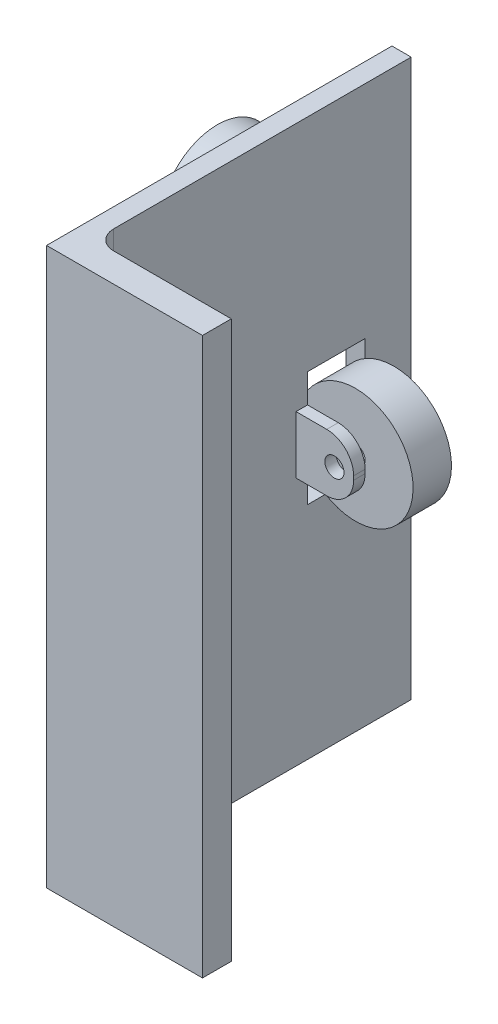
SolidWorks part; units mm, degrees
ref_plane "Front Plane" through (0, 0, 0) normal (0, 0, 1) x (1, 0, 0)
ref_plane "Top Plane" through (0, 0, 0) normal (0, 1, 0) x (1, 0, 0)
ref_plane "Right Plane" through (0, 0, 0) normal (1, 0, 0) x (0, 0, -1)
sketch "Sketch1" plane through (0, 0, 0) normal (0, 1, 0) x (1, 0, 0)
  line L0 (0, 0) -> (0, 90)
  line L1 (0, 90) -> (5, 90)
  line L2 (5, 90) -> (5, 12.5)
  line L3 (10, 7.5) -> (40.625, 7.5)
  line L4 (0, 0) -> (40.625, 0)
  line L5 (40.625, 0) -> (40.625, 7.5)
  arc A0 (5, 12.5) -> (10, 7.5) centre (10, 12.5) ccw
  dimension "D5" = 5
  dimension "D1" = 5
  dimension "D2" = 7.5
  dimension "D3" = 90
  dimension "D4" = 40.625
extrude "Boss-Extrude1" add sketch "Sketch1" along normal blind 145
sketch "Sketch3" plane through (0, 0, 0) normal (-1, 0, 0) x (0, 0, 1)
  line L0 (-90, 145) -> (-90, 0) construction
  line L1 (-90, 145) -> (0, 145) construction
  line L2 (-90, 72.5) -> (0, 72.5) construction
  line L3 (0, 145) -> (0, 0) construction
  circle A0 centre (-54.5, 125) radius 15
  circle A1 centre (-54.5, 20) radius 15
  dimension "D1" = 30
  dimension "D2" = 35.5
  dimension "D3" = 20
extrude "Boss-Extrude2" add sketch "Sketch3" along normal blind 10
sketch "Sketch4" plane through (0, 0, 0) normal (-1, 0, 0) x (0, 0, 1)
  line L2 (-90, 145) -> (-90, 0) construction
  line L3 (-70.5, 108.8445) -> (-70.5, 40.4519) construction
  line L4 (-78, 87.5) -> (-63, 87.5)
  line L5 (-78, 87.5) -> (-78, 57.5)
  line L6 (-78, 57.5) -> (-63, 57.5)
  line L7 (-63, 87.5) -> (-63, 57.5)
  line L8 (-90, 72.5) -> (0, 72.5) construction
  line L9 (0, 145) -> (0, 0) construction
  dimension "D1" = 19.5
  dimension "D2" = 15
  dimension "D3" = 30
extrude "Cut-Extrude1" cut sketch "Sketch4" against normal blind 10
ref_plane "Plane1" through (0, 0, -65.5) normal (0, 0, -1) x (-1, 0, 0)
sketch "Sketch6" plane through (0, 0, -65.5) normal (0, 0, -1) x (-1, 0, 0)
  line L1 (-5, 145) -> (-5, 0) construction
  circle A0 centre (-15, 72.5) radius 15
  dimension "D1" = 10
  dimension "D2" = 30
extrude "Boss-Extrude3" add sketch "Sketch6" along normal blind 10 separate body
sketch "Sketch7" plane through (5, 0, 0) normal (1, 0, 0) x (0, 0, -1)
  line L0 (81.6968, 72.5) -> (50.3125, 72.5) construction
  line L1 (70.5, 89.5858) -> (70.5, 52.0367) construction
  line L2 (81, 80) -> (81, 65)
  line L3 (63, 80) -> (60, 80)
  line L4 (63, 80) -> (63, 65)
  line L5 (63, 65) -> (60, 65)
  line L6 (60, 80) -> (60, 65)
  line L7 (78, 65) -> (81, 65)
  line L8 (78, 80) -> (78, 65)
  line L9 (78, 80) -> (81, 80)
  line L10 (63, 57.5) -> (63, 87.5) construction
  point P8 (66.0047, 72.5)
  dimension "D1" = 15
  dimension "D2" = 3
extrude "Boss-Extrude4" add sketch "Sketch7" along normal blind 15
fillet "Fillet1" radius 7 4 edges at (20, 80, -61.5) (20, 65, -61.5) (20, 80, -79.5) (20, 65, -79.5)
sketch "Sketch8" plane through (0, 0, -81) normal (0, 0, -1) x (-1, 0, 0)
  circle A0 centre (-15, 72.5) radius 2.5
  dimension "D1" = 5
extrude "Cut-Extrude2" cut sketch "Sketch8" against normal blind 25
